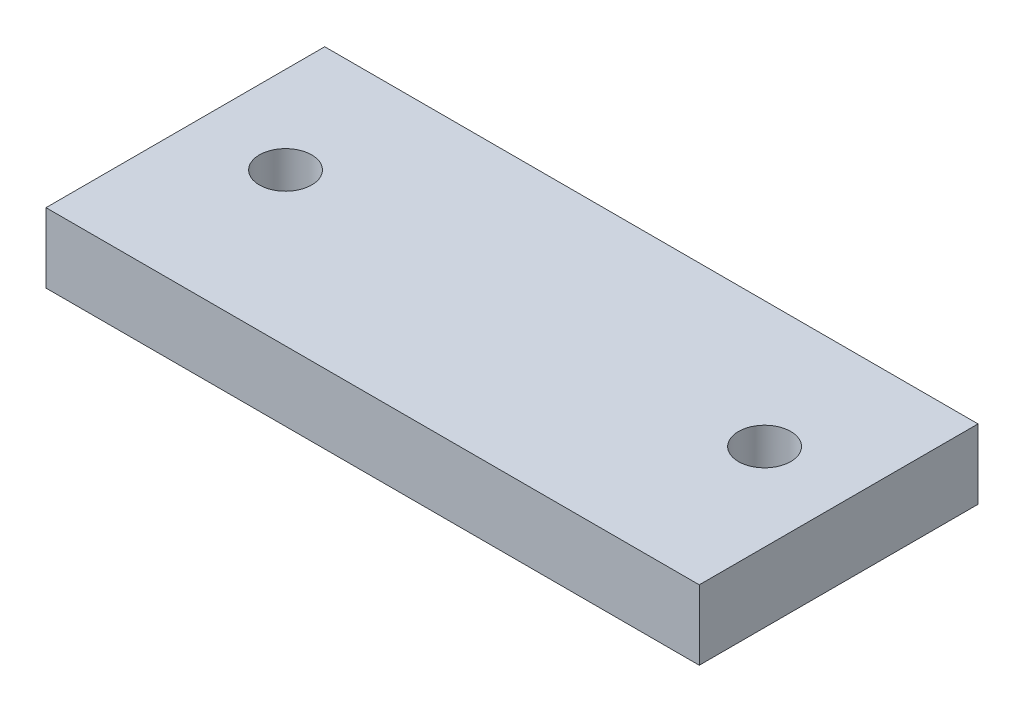
SolidWorks part; units mm, degrees
ref_plane "Front Plane" through (0, 0, 0) normal (0, 0, 1) x (1, 0, 0)
ref_plane "Top Plane" through (0, 0, 0) normal (0, 1, 0) x (1, 0, 0)
ref_plane "Right Plane" through (0, 0, 0) normal (1, 0, 0) x (0, 0, -1)
sketch "Sketch1" plane through (0, 0, 0) normal (0, 1, 0) x (1, 0, 0)
  line L1 (-7.5, -2) -> (7.5, -2)
  line L2 (-7.5, -2) -> (-7.5, 2)
  line L3 (-7.5, 2) -> (7.5, 2)
  line L4 (7.5, -2) -> (7.5, 2)
  line L5 (-7.5, -2) -> (7.5, 2) construction
  line L6 (-7.5, 2) -> (7.5, -2) construction
  point P0 (0, 0)
  dimension "D1" = 4
  dimension "D2" = 15
extrude "Boss-Extrude1" add sketch "Sketch1" along normal blind 1.6
sketch "Sketch5" plane through (0, 0, 2) normal (0, 0, 1) x (1, 0, 0)
  line L1 (-7.5, 1.6) -> (7.5, 1.6)
  line L2 (-7.5, 1.6) -> (-7.5, 0)
  line L3 (-7.5, 0) -> (7.5, 0)
  line L4 (7.5, 1.6) -> (7.5, 0)
extrude "Boss-Extrude4" add sketch "Sketch5" along normal blind 1.5
sketch "Sketch6" plane through (0, 0, -2) normal (0, 0, -1) x (-1, 0, 0)
  line L1 (7.5, 1.6) -> (-7.5, 1.6)
  line L2 (7.5, 1.6) -> (7.5, 0)
  line L3 (7.5, 0) -> (-7.5, 0)
  line L4 (-7.5, 1.6) -> (-7.5, 0)
extrude "Boss-Extrude5" add sketch "Sketch6" along normal blind 0.9
sketch "Sketch8" plane through (0, 1.6, 0) normal (0, 1, 0) x (1, 0, 0)
  line L0 (0, 0) -> (0, -3.5) construction
  line L1 (7.5, -3.5) -> (-7.5, -3.5) construction
  circle A0 centre (5.5, 0) radius 0.6
  circle A1 centre (-5.5, 0) radius 0.6
  dimension "D1" = 1.2
  dimension "D2" = 5.5
  dimension "D3" = 3.5
extrude "Cut-Extrude1" cut sketch "Sketch8" against normal blind 10
